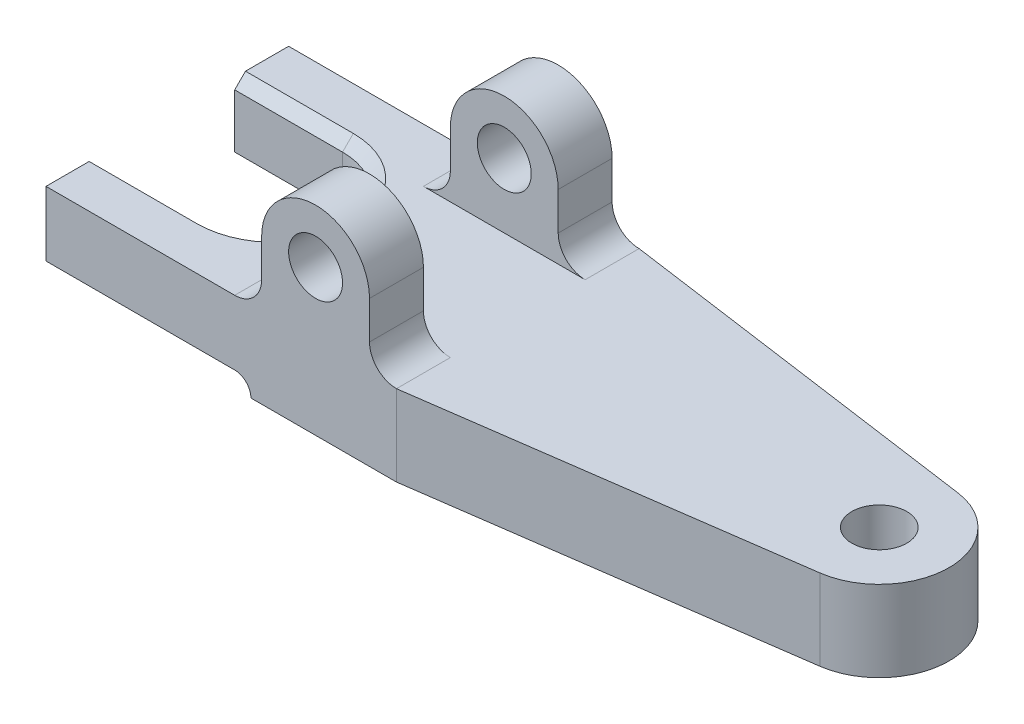
SolidWorks part; units mm, degrees
ref_plane "Płaszczyzna przednia" through (0, 0, 0) normal (0, 0, 1) x (1, 0, 0)
ref_plane "Płaszczyzna górna" through (0, 0, 0) normal (0, 1, 0) x (1, 0, 0)
ref_plane "Płaszczyzna prawa" through (0, 0, 0) normal (1, 0, 0) x (0, 0, -1)
sketch "Szkic1" plane through (0, 0, 0) normal (0, 1, 0) x (1, 0, 0)
  line L0 (-20, 12.5) -> (-20, 22.5)
  line L1 (-20, 22.5) -> (45, 22.5)
  line L2 (45, 22.5) -> (113.8528, 12.8234)
  line L3 (113.8528, -12.8234) -> (45, -22.5)
  line L4 (45, -22.5) -> (-20, -22.5)
  line L5 (-20, -22.5) -> (-20, -12.5)
  line L6 (-20, -12.5) -> (0, -12.5)
  line L7 (0, 12.5) -> (-20, 12.5)
  arc A0 (113.8528, 12.8234) -> (113.8528, -12.8234) centre (112.0506, 0) cw
  arc A1 (0, -12.5) -> (0, 12.5) centre (0, 0) ccw
  point P12 (0, 0)
  point P13 (0, 11.3513)
  point P15 (0, 0)
  point P16 (-26.0126, -7.8311)
  point P17 (0, 16.5095)
  point P18 (0, -7.9923)
  point P19 (24.5118, -22.5)
  point P20 (0, 0)
  point P21 (0, -11.0551)
  point P22 (67.5512, -12.5058)
  dimension "D1" = 45
  dimension "D2" = 25
  dimension "D3" = 20
  dimension "D4" = 8
  dimension "D5" = 145
extrude "Dodanie-wyciągnięcie1" add sketch "Szkic1" along normal blind 15
sketch "Szkic2" plane through (0, 0, 22.5) normal (0, 0, 1) x (1, 0, 0)
  line L0 (-20, 3) -> (15, 3)
  line L1 (-20, 15) -> (-20, 0) construction
  line L2 (-20, 0) -> (45, 0) construction
  line L3 (18, 0) -> (-20, 0)
  line L4 (-20, 0) -> (-20, 3)
  arc A0 (15, 3) -> (18, 0) centre (15, 0) cw
  point P8 (20.1178, 0)
  point P11 (0, 0)
  dimension "D2" = 35
  dimension "D1" = 3
extrude "Wytnij-wyciągnięcie1" cut sketch "Szkic2" against normal through all
sketch "Szkic3" plane through (0, 0, 22.5) normal (0, 0, 1) x (1, 0, 0)
  line L0 (20, 15) -> (20, 27)
  line L1 (-20, 15) -> (45, 15) construction
  line L2 (40, 27) -> (40, 15)
  line L3 (40, 15) -> (20, 15)
  line L4 (-20, 15) -> (-20, 3) construction
  arc A0 (20, 27) -> (40, 27) centre (30, 27) cw
  circle A1 centre (30, 27) radius 5
  dimension "D1" = 10
  dimension "D4" = 10
  dimension "D2" = 12
  dimension "D3" = 50
extrude "Dodanie-wyciągnięcie2" add sketch "Szkic3" against normal blind 10
fillet "Zaokrąglenie1" radius 5 2 edges at (40, 15, 17.5) (20, 15, 17.5)
mirror "Lustro1" about plane through (0, 0, 0) normal (0, 0, 1) of "Zaokrąglenie1", "Dodanie-wyciągnięcie2"
chamfer "Sfazowanie1" distance 2 angle 45 3 edges at (-10, 15, 12.5) (12.5, 15, 0) (-10, 15, -12.5)
hole_wizard "Otwór gwintowany M121" positions "Szkic4" profile "Szkic5" tap size "M12" standard "ISO" end condition through all
sketch "Szkic4" plane through (0, 15, 0) normal (0, 1, 0) x (1, 0, 0)
  arc A0 (113.8528, -12.8234) -> (113.8528, 12.8234) centre (112.0506, 0) ccw construction
  point P0 (112.0506, 0)
  point P3 (0, 0)
sketch "Szkic5" plane through (112.0506, 15, 0) normal (1, 0, 0) x (0, 0, 1)
  line L0 (0, 0) -> (0, 15)
  line L1 (0, 15) -> (5.1, 15)
  line L2 (5.1, 15) -> (5.1, 0)
  line L5 (5.1, 0) -> (0, 0)
  line L11 (0, -6.35) -> (0, 107.95) construction
  dimension "Średnica otworu gwintowanego na wylot" = 10.2
  dimension "Głębokość otworu gwintowanego na wylot" = 15
cosmetic thread "Gwint otworu1" parameters "D2"=12
